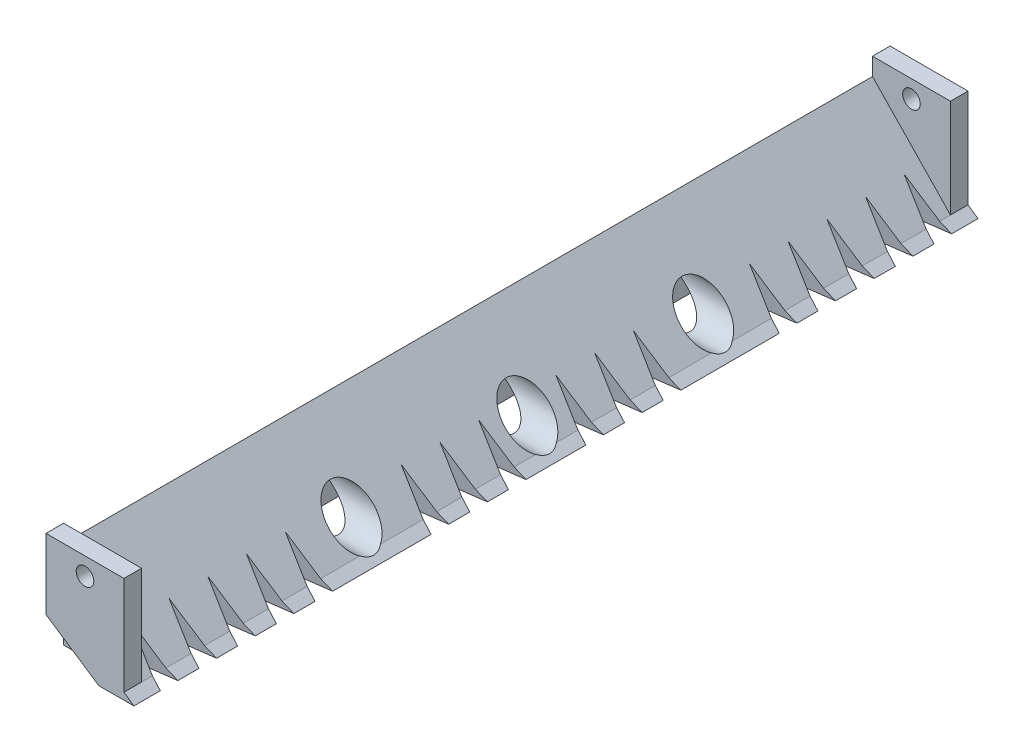
SolidWorks part; units mm, degrees
ref_plane "Front Plane" through (0, 0, 0) normal (0, 0, 1) x (1, 0, 0)
ref_plane "Top Plane" through (0, 0, 0) normal (0, 1, 0) x (1, 0, 0)
ref_plane "Right Plane" through (0, 0, 0) normal (1, 0, 0) x (0, 0, -1)
sketch "Sketch1" plane through (0, 0, 0) normal (0, 0, 1) x (1, 0, 0)
  line L0 (0, 0) -> (50, -35)
  line L1 (50, -35) -> (30, -35)
  line L2 (30, -35) -> (0, -15)
  line L3 (0, -15) -> (0, 0)
  dimension "D1" = 50
  dimension "D2" = 30
  dimension "D3" = 20
  dimension "D4" = 35
extrude "Boss-Extrude1" add sketch "Sketch1" along normal blind 480
ref_plane "Plane1" through (0, 0, 240) normal (0, 0, 1) x (1, 0, 0)
sketch "Sketch2" plane through (0, 0, 480) normal (0, 0, 1) x (1, 0, 0)
  line L0 (0, 15) -> (44.3497, 15) construction
  line L1 (0, -15) -> (44.3497, -15) construction
  line L2 (0, -15) -> (0, 25)
  line L3 (0, 25) -> (44.3497, 25)
  line L4 (44.3497, -15) -> (44.3497, 25)
  line L5 (44.3497, -15) -> (44.3497, -35)
  line L6 (30, -35) -> (50, -35) construction
  line L7 (44.3497, -35) -> (30, -35)
  line L8 (30, -35) -> (0, -15)
  circle A0 centre (22.1748, 15) radius 5
  dimension "D2" = 10
  dimension "D3" = 10
  dimension "D1" = 40
extrude "Boss-Extrude2" add sketch "Sketch2" against normal blind 10
mirror "Mirror1" about plane through (0, 0, 240) normal (0, 0, 1) of "Boss-Extrude2"
sketch "Sketch4" plane through (0, 0, 480) normal (0, 0, 1) x (1, 0, 0)
  line L0 (0, 0) -> (0, 15)
  line L1 (0, 25) -> (0, -15) construction
  line L2 (0, 15) -> (44.3497, -31.0448)
  line L3 (44.3497, -31.0448) -> (0, 0)
  dimension "D1" = 15
extrude "Boss-Extrude3" add sketch "Sketch4" against normal through all
sketch "Sketch3" plane through (0, 0, 0) normal (0.5735, 0.8192, 0) x (0.8192, -0.5735, 0)
  line L0 (61.0328, -465) -> (31.0328, -460)
  line L1 (61.0328, -480) -> (61.0328, 0) construction
  line L2 (31.0328, -460) -> (61.0328, -455)
  line L3 (31.0328, -460) -> (61.0328, -460) construction
  line L4 (61.0328, -465) -> (61.0328, -455)
  line L5 (61.0328, -443) -> (31.0328, -438)
  line L6 (31.0328, -438) -> (61.0328, -433)
  line L7 (61.0328, -443) -> (61.0328, -433)
  line L8 (61.0328, -421) -> (31.0328, -416)
  line L9 (31.0328, -416) -> (61.0328, -411)
  line L10 (61.0328, -421) -> (61.0328, -411)
  line L11 (61.0328, -399) -> (31.0328, -394)
  line L12 (31.0328, -394) -> (61.0328, -389)
  line L13 (61.0328, -399) -> (61.0328, -389)
  line L14 (61.0328, -377) -> (31.0328, -372)
  line L15 (31.0328, -372) -> (61.0328, -367)
  line L16 (61.0328, -377) -> (61.0328, -367)
  line L17 (61.0328, -355) -> (31.0328, -350) construction
  line L18 (31.0328, -350) -> (61.0328, -345) construction
  line L19 (61.0328, -355) -> (61.0328, -345) construction
  line L20 (61.0328, -333) -> (31.0328, -328) construction
  line L21 (31.0328, -328) -> (61.0328, -323) construction
  line L22 (61.0328, -333) -> (61.0328, -323) construction
  line L23 (61.0328, -311) -> (31.0328, -306)
  line L24 (31.0328, -306) -> (61.0328, -301)
  line L25 (61.0328, -311) -> (61.0328, -301)
  line L26 (61.0328, -289) -> (31.0328, -284)
  line L27 (31.0328, -284) -> (61.0328, -279)
  line L28 (61.0328, -289) -> (61.0328, -279)
  line L29 (61.0328, -267) -> (31.0328, -262)
  line L30 (31.0328, -262) -> (61.0328, -257)
  line L31 (61.0328, -267) -> (61.0328, -257)
  line L32 (61.0328, -245) -> (31.0328, -240) construction
  line L33 (31.0328, -240) -> (61.0328, -235) construction
  line L34 (61.0328, -245) -> (61.0328, -235) construction
  line L35 (61.0328, -223) -> (31.0328, -218)
  line L36 (31.0328, -218) -> (61.0328, -213)
  line L37 (61.0328, -223) -> (61.0328, -213)
  line L38 (61.0328, -201) -> (31.0328, -196)
  line L39 (31.0328, -196) -> (61.0328, -191)
  line L40 (61.0328, -201) -> (61.0328, -191)
  line L41 (61.0328, -179) -> (31.0328, -174)
  line L42 (31.0328, -174) -> (61.0328, -169)
  line L43 (61.0328, -179) -> (61.0328, -169)
  line L44 (61.0328, -157) -> (31.0328, -152) construction
  line L45 (31.0328, -152) -> (61.0328, -147) construction
  line L46 (61.0328, -157) -> (61.0328, -147) construction
  line L47 (61.0328, -135) -> (31.0328, -130) construction
  line L48 (31.0328, -130) -> (61.0328, -125) construction
  line L49 (61.0328, -135) -> (61.0328, -125) construction
  line L50 (61.0328, -113) -> (31.0328, -108)
  line L51 (31.0328, -108) -> (61.0328, -103)
  line L52 (61.0328, -113) -> (61.0328, -103)
  line L53 (61.0328, -91) -> (31.0328, -86)
  line L54 (31.0328, -86) -> (61.0328, -81)
  line L55 (61.0328, -91) -> (61.0328, -81)
  line L56 (61.0328, -69) -> (31.0328, -64)
  line L57 (31.0328, -64) -> (61.0328, -59)
  line L58 (61.0328, -69) -> (61.0328, -59)
  line L59 (61.0328, -47) -> (31.0328, -42)
  line L60 (31.0328, -42) -> (61.0328, -37)
  line L61 (61.0328, -47) -> (61.0328, -37)
  line L62 (61.0328, -25) -> (31.0328, -20)
  line L63 (31.0328, -20) -> (61.0328, -15)
  line L64 (61.0328, -25) -> (61.0328, -15)
  dimension "D1" = 5
  dimension "D2" = 5
  dimension "D3" = 15
  dimension "D4" = 30
  dimension "D5" = 21
extrude "Cut-Extrude9" cut sketch "Sketch3" against normal mid plane 56
sketch "Sketch14" plane through (0, 0, 0) normal (-1, 0, 0) x (0, 0, 1)
  line L0 (10, 0) -> (470, 0)
  line L1 (10, 15) -> (470, 15) construction
  line L2 (10, 0) -> (10, -35)
  line L3 (10, -35) -> (470, -35)
  line L4 (470, 0) -> (470, -35)
  dimension "D1" = 460
  dimension "D2" = 50
extrude "Boss-Extrude6" add sketch "Sketch14" against normal blind 5
sketch "Sketch7" plane through (0, 0, 0) normal (-1, 0, 0) x (0, 0, 1)
  line L0 (0, -20) -> (480, -20) construction
  line L1 (0, 25) -> (0, -15) construction
  line L2 (480, 25) -> (480, -15) construction
  line L3 (10, 15) -> (470, 15) construction
  circle A0 centre (240, -20) radius 12.5
  circle A1 centre (340, -20) radius 12.5
  circle A2 centre (140, -20) radius 12.5
  dimension "D1" = 25
  dimension "D3" = 100
  dimension "D2" = 35
  dimension "D4" = 100
extrude "Cut-Extrude8" cut sketch "Sketch7" against normal blind 56
sketch "Sketch15" plane through (0, 0, 0) normal (-1, 0, 0) x (0, 0, 1)
  line L0 (240, 15) -> (240, -35) construction
  line L1 (10, 15) -> (470, 15) construction
  line L2 (10, -35) -> (470, -35) construction
  line L3 (140, -20) -> (340, -20) construction
  circle A0 centre (240, -20) radius 9
  circle A1 centre (140, -20) radius 9
  circle A2 centre (340, -20) radius 9
  circle A3 centre (340, -20) radius 12.5
  circle A4 centre (240, -20) radius 12.5
  circle A5 centre (140, -20) radius 12.5
  dimension "D1" = 35
  dimension "D2" = 18
  dimension "D3" = 100
  dimension "D4" = 100
extrude "Boss-Extrude7" add sketch "Sketch15" against normal blind 5
